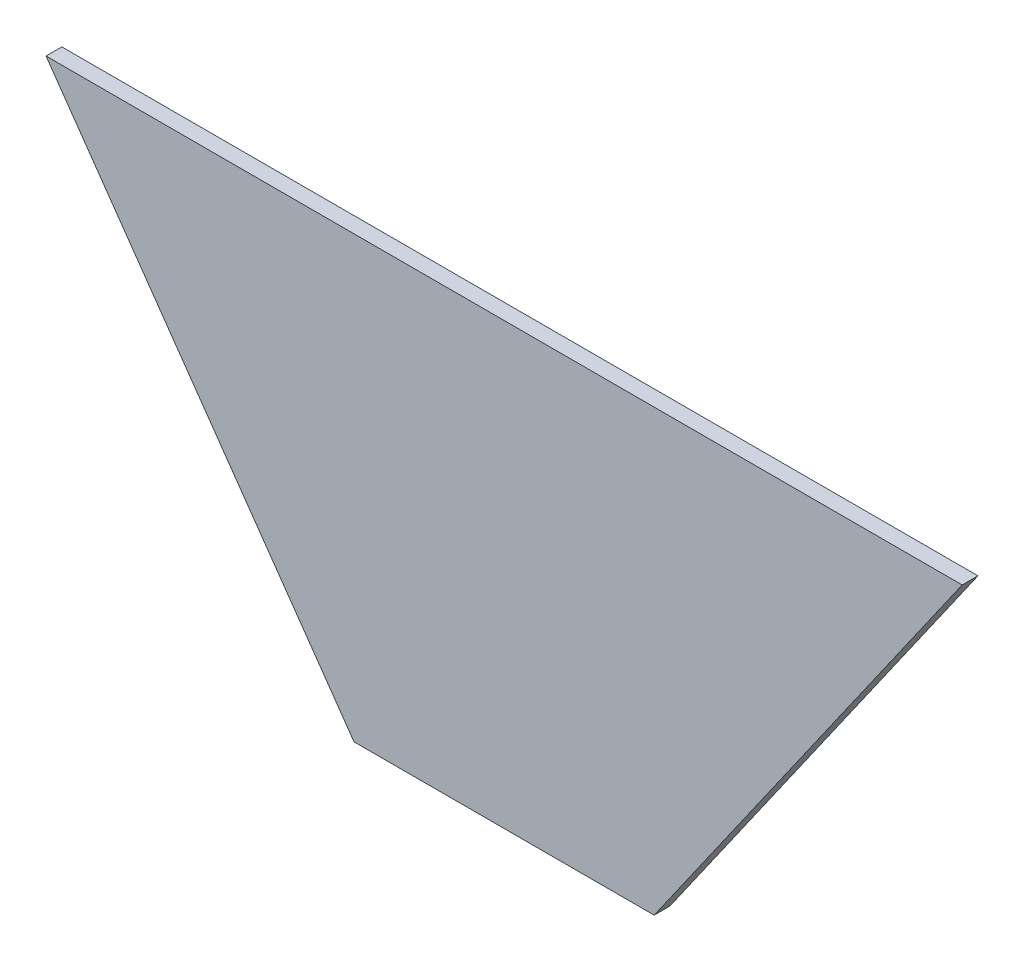
SolidWorks part; units mm, degrees
ref_plane "Front Plane" through (0, 0, 0) normal (0, 0, 1) x (1, 0, 0)
ref_plane "Top Plane" through (0, 0, 0) normal (0, 1, 0) x (1, 0, 0)
ref_plane "Right Plane" through (0, 0, 0) normal (1, 0, 0) x (0, 0, -1)
sketch "Sketch1" plane through (0, 0, 0) normal (0, 0, 1) x (1, 0, 0)
  line L0 (-95, 0) -> (95, 0)
  line L1 (95, 0) -> (290, 278.5229)
  line L2 (290, 278.5229) -> (-290, 278.5229)
  line L3 (-290, 278.5229) -> (-95, 0)
  point P3 (0, 0)
  dimension "D1" = 190
  dimension "D2" = 580
  dimension "D3" = 340
  dimension "D4" = 340
extrude "Boss-Extrude1" add sketch "Sketch1" along normal blind 10
